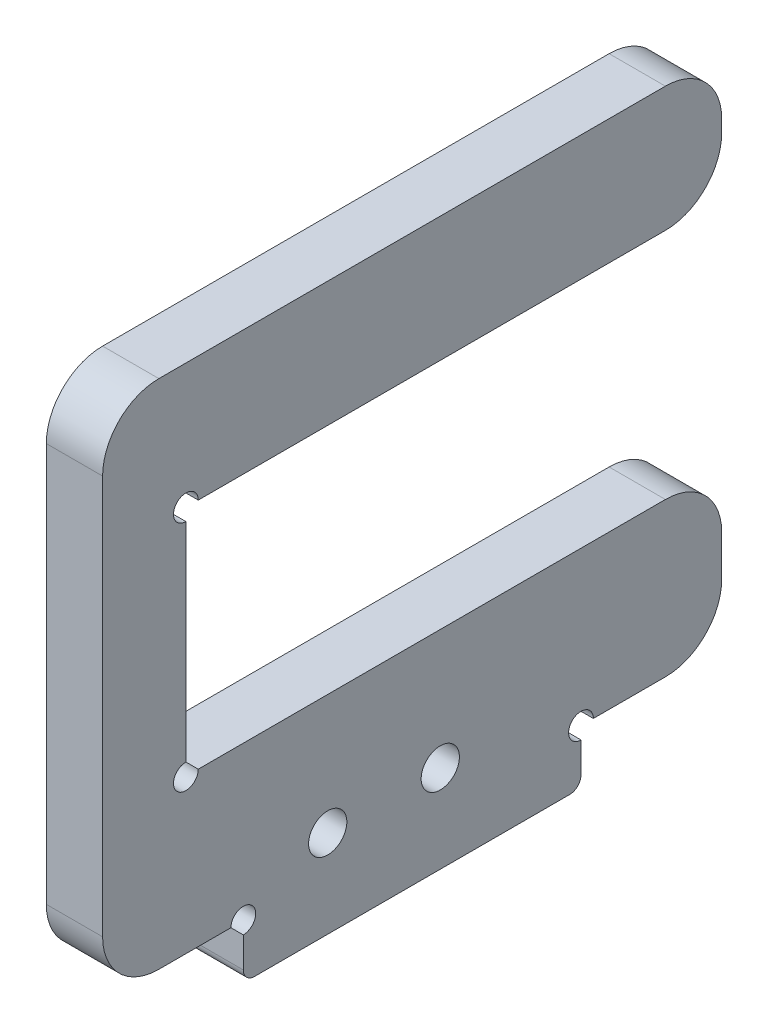
SolidWorks part; units mm, degrees
ref_plane "前视基准面" through (0, 0, 0) normal (0, 0, 1) x (1, 0, 0)
ref_plane "上视基准面" through (0, 0, 0) normal (0, 1, 0) x (1, 0, 0)
ref_plane "右视基准面" through (0, 0, 0) normal (1, 0, 0) x (0, 0, -1)
other "Configuration Table"
sketch "草图1" plane through (0, 0, 0) normal (1, 0, 0) x (0, 0, -1)
  line L0 (7.5, 13.75) -> (0, 13.75) construction
  line L1 (0, 0) -> (55, 0)
  line L2 (0, 0) -> (0, 45.45)
  line L3 (0, 45.45) -> (55, 45.45)
  line L4 (55, 0) -> (55, 45.45)
  line L5 (7.5, 34.25) -> (47.5, 34.25) construction
  line L6 (7.5, 34.25) -> (7.5, 13.75) construction
  line L7 (7.5, 13.75) -> (47.5, 13.75) construction
  line L8 (47.5, 34.25) -> (47.5, 13.75) construction
  line L9 (47.5, 13.75) -> (55, 13.75) construction
  line L10 (7.4, 34.35) -> (47.6, 34.35)
  line L11 (47.6, 34.35) -> (47.6, 13.65)
  line L12 (7.4, 13.65) -> (47.6, 13.65)
  line L13 (7.4, 34.35) -> (7.4, 13.65)
  dimension "D1" = 40
  dimension "D2" = 20.5
  dimension "D3" = 13.75
  dimension "D4" = 45.45
  dimension "D5" = 55
  dimension "D6" = 0.1
extrude "凸台-拉伸1" add sketch "草图1" along normal blind 5
sketch "草图2" plane through (0, 0, 0) normal (-1, 0, 0) x (0, 0, 1)
  line L0 (0, 0) -> (-55, 0) construction
  line L1 (-42.5, 0) -> (-12.5, 0)
  line L2 (-42.5, 0) -> (-42.5, -4.8)
  line L3 (-42.5, -4.8) -> (-12.5, -4.8)
  line L4 (-12.5, 0) -> (-12.5, -4.8)
  dimension "D1" = 30
  dimension "D2" = 4.8
  dimension "D3" = 12.5
extrude "凸台-拉伸2" add sketch "草图2" against normal blind 5
sketch "草图3" plane through (0, 0, 0) normal (-1, 0, 0) x (0, 0, 1)
  circle A0 centre (-42.5, 0) radius 1.1
  circle A1 centre (-12.5, 0) radius 1.1
  circle A4 centre (-7.4, 13.65) radius 1.1
  circle A5 centre (-7.4, 34.35) radius 1.1
  dimension "D1" = 2.2
extrude "切除-拉伸1" cut sketch "草图3" against normal blind 5
fillet "圆角2" radius 5 4 edges at (2.5, 0, 0) (2.5, 45.45, 0) (2.5, 45.45, -55) (2.5, 0, -55)
fillet "圆角3" radius 1 2 edges at (2.5, -4.8, -12.5) (2.5, -4.8, -42.5)
hole_wizard "M3 Clearance Hole1" positions "Sketch1" profile "Sketch2" hole size "M3" standard "GB" end condition through all
sketch "Sketch1" plane through (0, 0, 0) normal (-1, 0, 0) x (0, 0, 1)
  line L0 (-55, 5) -> (-55, 40.45) construction
  line L1 (-43.6, 0) -> (-50, 0) construction
  point P0 (-30, 3)
  point P2 (-20, 3)
  dimension "D1" = 25
  dimension "D2" = 35
  dimension "D3" = 3
  dimension "D4" = 3
sketch "Sketch2" plane through (0, 3, -30) normal (0, 1, 0) x (0, 0, 1)
  line L0 (0, 0) -> (0, 5)
  line L1 (0, 5) -> (1.7, 5)
  line L2 (1.7, 5) -> (1.7, 0)
  line L5 (1.7, 0) -> (0, 0)
  line L11 (0, -6.35) -> (0, 107.95) construction
  dimension "Thru Hole Dia." = 3.4
  dimension "Thru Hole Depth" = 5
sketch "Sketch3" plane through (0, 0, 0) normal (-1, 0, 0) x (0, 0, 1)
  line L0 (-55, 5) -> (-55, 40.45) construction
  line L1 (-47.6, 34.35) -> (-55, 34.35)
  line L2 (-47.6, 34.35) -> (-47.6, 13.65)
  line L3 (-47.6, 13.65) -> (-55, 13.65)
  line L4 (-55, 34.35) -> (-55, 13.65)
  line L5 (-8.5, 13.65) -> (-47.6, 13.65) construction
  line L6 (-47.6, 34.35) -> (-8.5, 34.35) construction
  dimension "D1" = 7.4
extrude "Cut-Extrude1" cut sketch "Sketch3" against normal blind 10
fillet "Fillet1" radius 5 2 edges at (2.5, 34.35, -55) (2.5, 13.65, -55)
